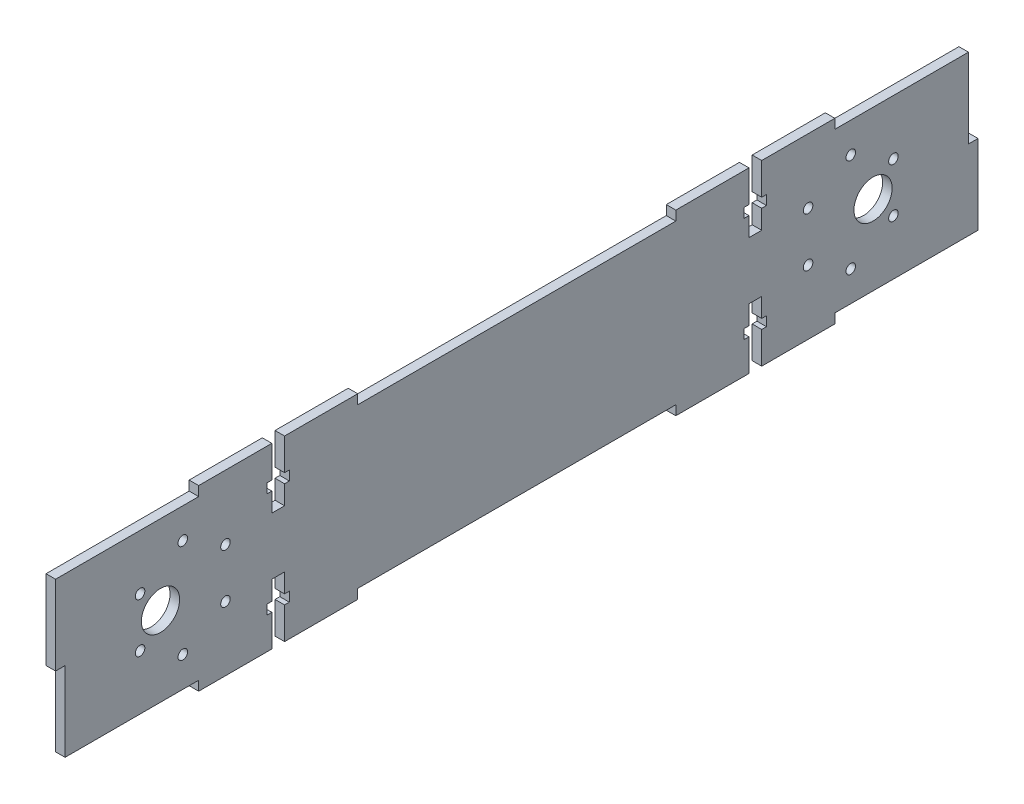
SolidWorks part; units mm, degrees
ref_plane "Front Plane" through (0, 0, 0) normal (0, 0, 1) x (1, 0, 0)
ref_plane "Top Plane" through (0, 0, 0) normal (0, 1, 0) x (1, 0, 0)
ref_plane "Right Plane" through (0, 0, 0) normal (1, 0, 0) x (0, 0, -1)
sketch "Sketch1" plane through (0, 0, 0) normal (1, 0, 0) x (0, 0, -1)
  line L0 (-145, 0) -> (-142, 0)
  line L1 (-145, 25) -> (-100, 25)
  line L2 (-145, 25) -> (-145, 0)
  line L3 (-142, -25) -> (-100, -25)
  line L4 (145, 0) -> (145, -25)
  line L5 (-145, 25) -> (145, -25) construction
  line L6 (-145, -25) -> (145, 25) construction
  line L7 (-142, 0) -> (-142, -25)
  line L8 (145, 0) -> (142, 0)
  line L9 (142, 0) -> (142, 25)
  line L10 (-145, 25) -> (-145, 60.1701) construction
  line L11 (-145, 60.1701) -> (-100, 60.1701) construction
  line L12 (-100, 60.1701) -> (-100, 65.1701) construction
  line L13 (-100, 65.1701) -> (-50, 65.1701) construction
  line L14 (-50, 65.1701) -> (-50, 60.1701) construction
  line L15 (-50, 60.1701) -> (50, 60.1701) construction
  line L16 (50, 60.1701) -> (50, 65.1701) construction
  line L17 (50, 65.1701) -> (100, 65.1701) construction
  line L18 (100, 65.1701) -> (100, 60.1701) construction
  line L19 (100, 60.1701) -> (145, 60.1701) construction
  line L20 (-100, 25) -> (-100, 28)
  line L21 (-100, 28) -> (-50, 28)
  line L22 (-50, 28) -> (-50, 25)
  line L23 (50, 25) -> (50, 28)
  line L24 (50, 28) -> (100, 28)
  line L25 (100, 28) -> (100, 25)
  line L26 (-100, -25) -> (-100, -28)
  line L27 (-100, -28) -> (-50, -28)
  line L28 (-50, -28) -> (-50, -25)
  line L29 (50, -25) -> (50, -28)
  line L30 (50, -28) -> (100, -28)
  line L31 (100, -28) -> (100, -25)
  line L32 (-50, 25) -> (50, 25)
  line L33 (-50, -25) -> (50, -25)
  line L34 (100, 25) -> (142, 25)
  line L35 (100, -25) -> (145, -25)
  line L36 (-145, 60.1701) -> (-145, 70.065) construction
  line L37 (-145, 70.065) -> (-105, 70.065) construction
  line L38 (-105, 70.065) -> (-105, 0) construction
  line L39 (-105, 0) -> (-112, 0) construction
  line L40 (0, 25) -> (0, -25) construction
  circle A0 centre (-112, 0) radius 6
  circle A1 centre (112, 0) radius 6
  circle A2 centre (-105, 15.5) radius 1.5
  circle A3 centre (-91.5766, 7.75) radius 1.5
  circle A4 centre (-91.5766, -7.75) radius 1.5
  circle A5 centre (-105, -15.5) radius 1.5
  circle A6 centre (-118.4234, -7.75) radius 1.5
  circle A7 centre (-118.4234, 7.75) radius 1.5
  circle A8 centre (118.4234, -7.75) radius 1.5
  circle A9 centre (105, -15.5) radius 1.5
  circle A10 centre (91.5766, -7.75) radius 1.5
  circle A11 centre (91.5766, 7.75) radius 1.5
  circle A12 centre (105, 15.5) radius 1.5
  circle A13 centre (118.4234, 7.75) radius 1.5
  point P0 (0, 0)
  point P59 (-105, 0)
  dimension "D1" = 6
extrude "Boss-Extrude1" add sketch "Sketch1" along normal blind 3
sketch "Sketch2" plane through (3, 0, 0) normal (1, 0, 0) x (0, 0, -1)
  line L0 (-75, 28) -> (-73, 28)
  line L1 (-73, -28) -> (-73, -18)
  line L2 (-50, 28) -> (-100, 28) construction
  line L3 (-73, 28) -> (-73, 18)
  line L4 (-73, 18) -> (-71.5, 18)
  line L5 (-71.5, 18) -> (-71.5, 15)
  line L6 (-71.5, 15) -> (-73, 15)
  line L7 (-73, 15) -> (-73, 9)
  line L8 (-73, 9) -> (-77, 9)
  line L9 (-77, 9) -> (-77, 15)
  line L10 (-77, 15) -> (-78.5, 15)
  line L11 (-78.5, 15) -> (-78.5, 18)
  line L12 (-78.5, 18) -> (-77, 18)
  line L13 (-77, 18) -> (-77, 28)
  line L14 (-77, 28) -> (-75, 28)
  line L15 (-100, -28) -> (-50, -28) construction
  line L16 (-73, -18) -> (-71.5, -18)
  line L17 (-71.5, -18) -> (-71.5, -15)
  line L18 (-71.5, -15) -> (-73, -15)
  line L19 (-73, -15) -> (-73, -9)
  line L20 (-73, -9) -> (-77, -9)
  line L21 (-77, -9) -> (-77, -15)
  line L22 (-77, -15) -> (-78.5, -15)
  line L23 (-78.5, -15) -> (-78.5, -18)
  line L24 (-78.5, -18) -> (-77, -18)
  line L25 (-77, -18) -> (-77, -28)
  line L26 (-77, -28) -> (-73, -28)
  line L27 (75, -28) -> (77, -28)
  line L28 (50, -28) -> (100, -28) construction
  line L29 (77, -28) -> (77, -18)
  line L30 (77, -18) -> (78.5, -18)
  line L31 (78.5, -18) -> (78.5, -15)
  line L32 (78.5, -15) -> (77, -15)
  line L33 (77, -15) -> (77, -9)
  line L34 (77, -9) -> (73, -9)
  line L35 (73, -9) -> (73, -15)
  line L36 (73, -15) -> (71.5, -15)
  line L37 (71.5, -15) -> (71.5, -18)
  line L38 (71.5, -18) -> (73, -18)
  line L39 (73, -18) -> (73, -28)
  line L40 (73, -28) -> (75, -28)
  line L41 (77, 28) -> (77, 18)
  line L42 (100, 28) -> (50, 28) construction
  line L43 (77, 18) -> (78.5, 18)
  line L44 (78.5, 18) -> (78.5, 15)
  line L45 (78.5, 15) -> (77, 15)
  line L46 (77, 15) -> (77, 9)
  line L47 (77, 9) -> (73, 9)
  line L48 (73, 9) -> (73, 15)
  line L49 (73, 15) -> (71.5, 15)
  line L50 (71.5, 15) -> (71.5, 18)
  line L51 (71.5, 18) -> (73, 18)
  line L52 (73, 18) -> (73, 28)
  line L53 (73, 28) -> (77, 28)
extrude "Cut-Extrude1" cut sketch "Sketch2" against normal blind 3
